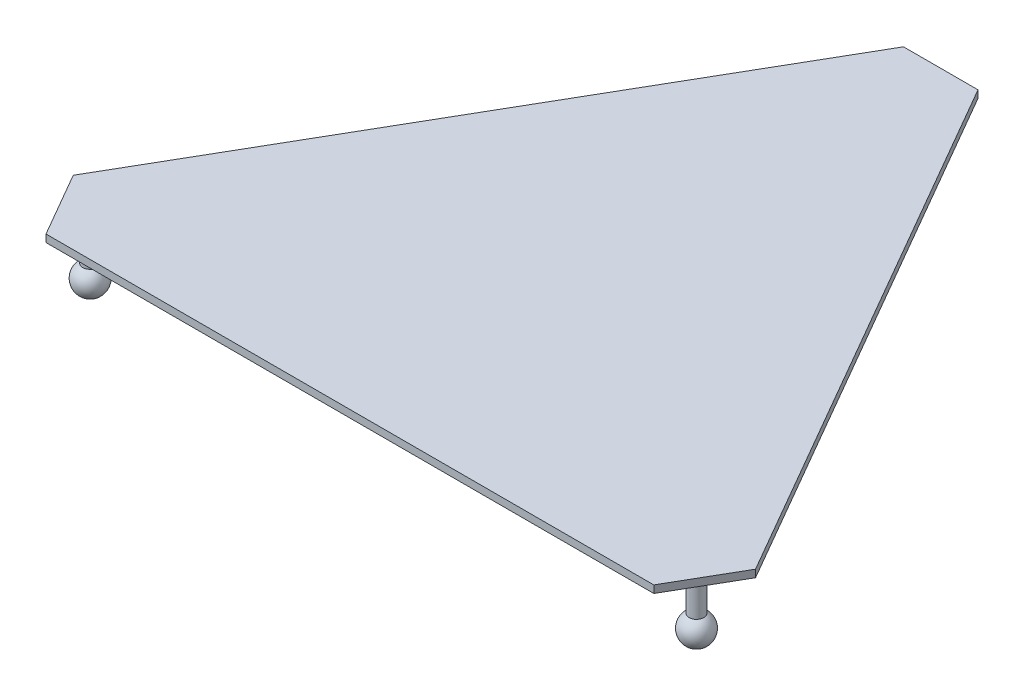
SolidWorks part; units mm, degrees
ref_plane "Alzado" through (0, 0, 0) normal (0, 0, 1) x (1, 0, 0)
ref_plane "Planta" through (0, 0, 0) normal (0, 1, 0) x (1, 0, 0)
ref_plane "Vista lateral" through (0, 0, 0) normal (1, 0, 0) x (0, 0, -1)
sketch "Croquis1" plane through (0, 0, 0) normal (0, 1, 0) x (1, 0, 0)
  line L0 (0, 0) -> (0, 500) construction
  line L2 (-50, 500) -> (50, 500)
  line L4 (0, 0) -> (433.0127, -250) construction
  line L9 (458.0127, -206.6987) -> (408.0127, -293.3013)
  line L11 (0, 0) -> (-433.0127, -250) construction
  line L12 (-408.0127, -293.3013) -> (-458.0127, -206.6987)
  line L13 (-50, 500) -> (-458.0127, -206.6987)
  line L14 (408.0127, -293.3013) -> (-408.0127, -293.3013)
  line L15 (458.0127, -206.6987) -> (50, 500)
  circle A0 centre (0, 0) radius 470 construction
  point P7 (0, 375)
  point P9 (0, 500)
  point P15 (0, 0)
  point P19 (0, 0)
  dimension "D1" = 470
  dimension "D3" = 100
  dimension "D2" = 500
  dimension "D4" = 3
extrude "Saliente-Extruir1" add sketch "Croquis1" along normal blind 10
sketch "Croquis2" plane through (0, 0, 0) normal (1, 0, 0) x (0, 0, -1)
  line L0 (0, 0) -> (470, 0) construction
  line L1 (-206.6987, 0) -> (500, 0) construction
  line L2 (470, 0) -> (470, -70)
  line L3 (480, -52.6795) -> (480, 0)
  line L4 (480, 0) -> (470, 0)
  line L5 (470, -70) -> (470, -90)
  arc A0 (470, -90) -> (480, -52.6795) centre (470, -70) ccw
  dimension "D2" = 40
  dimension "D1" = 470
  dimension "D3" = 70
  dimension "D4" = 10
revolve "Revolución1" add sketch "Croquis2" angle 360 about L2
sketch "Croquis3" plane through (0, 0, 0) normal (1, 0, 0) x (0, 0, -1)
  line L0 (0, -1000) -> (0, 49000) construction
pattern_circular "MatrizC1" count 3 every 120 about axis through (0, 0, 0) along (0, 1, 0) of "Revolución1"
